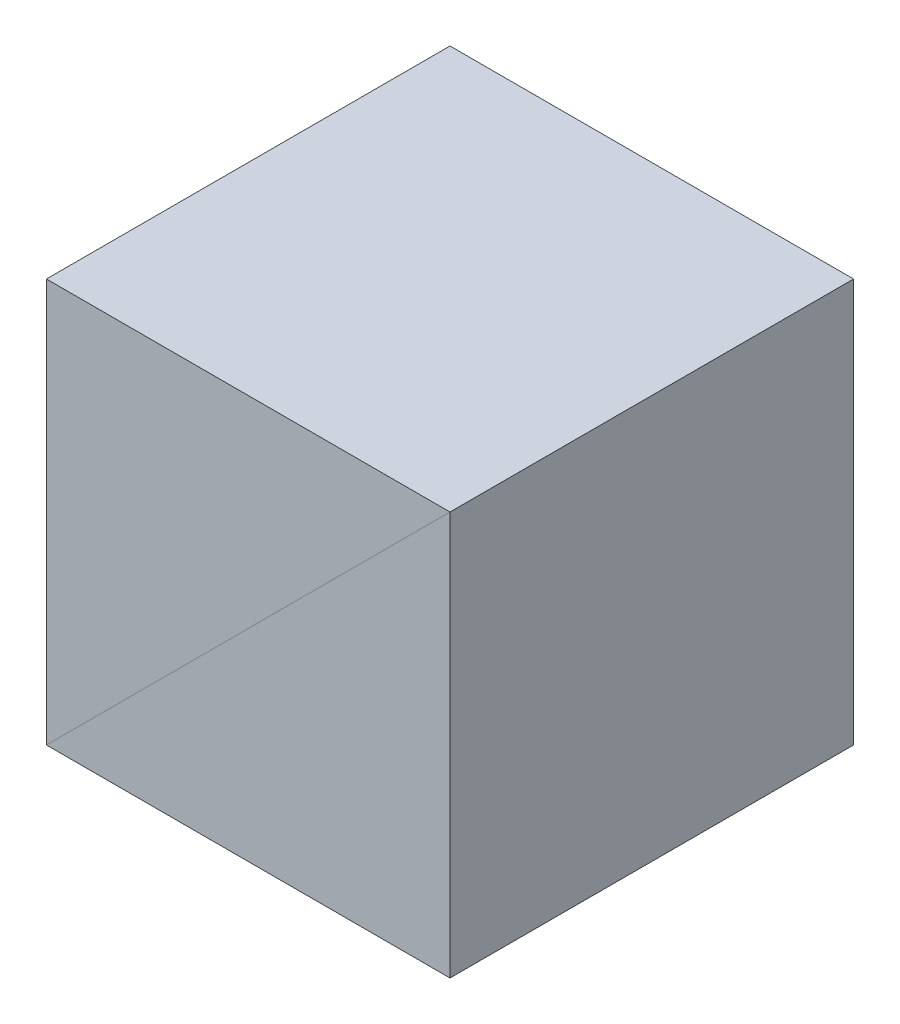
SolidWorks part; units mm, degrees
ref_plane "前视基准面" through (0, 0, 0) normal (0, 0, 1) x (1, 0, 0)
ref_plane "上视基准面" through (0, 0, 0) normal (0, 1, 0) x (1, 0, 0)
ref_plane "右视基准面" through (0, 0, 0) normal (1, 0, 0) x (0, 0, -1)
sketch "草图1" plane through (0, 0, 0) normal (0, 0, 1) x (1, 0, 0)
  line L3 (-12.7, -12.7) -> (12.7, -12.7)
  line L4 (12.7, 12.7) -> (12.7, -12.7)
  line L5 (12.7, 12.7) -> (-12.7, -12.7)
  dimension "D1" = 25.4
extrude "凸台-拉伸1" add sketch "草图1" along normal mid plane 25.4
mirror "镜向2" about plane through (12.7, 12.7, 12.7) normal (0.7071, -0.7071, 0) of bodies 107
